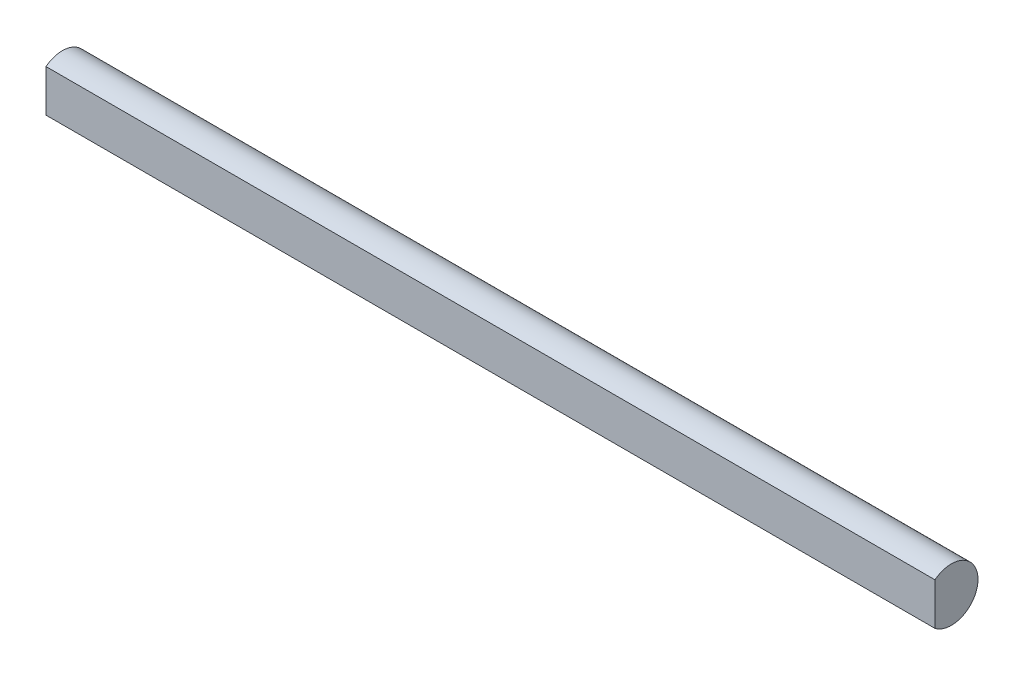
SolidWorks part; units mm, degrees
ref_plane "Front Plane" through (0, 0, 0) normal (0, 0, 1) x (1, 0, 0)
ref_plane "Top Plane" through (0, 0, 0) normal (0, 1, 0) x (1, 0, 0)
ref_plane "Right Plane" through (0, 0, 0) normal (1, 0, 0) x (0, 0, -1)
sketch "Sketch1" plane through (0, 0, 0) normal (1, 0, 0) x (0, 0, -1)
  line L0 (-1.7493, 2.25) -> (-1.7493, -2.25)
  arc A0 (-1.7493, -2.25) -> (-1.7493, 2.25) centre (0, 0) ccw
  dimension "D1" = 5.7
  dimension "D2" = 4.5
extrude "Boss-Extrude1" add sketch "Sketch1" along normal blind 95
